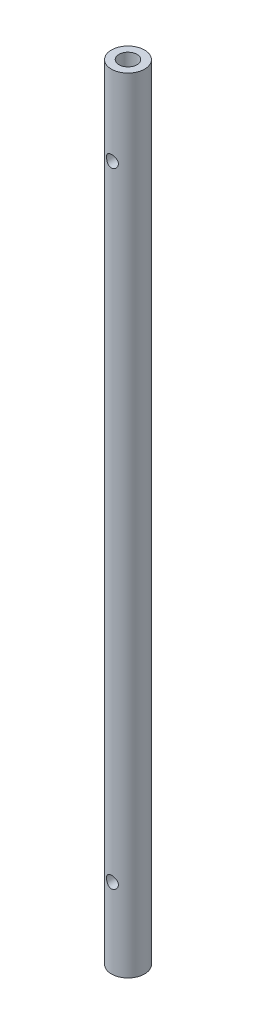
SolidWorks part; units mm, degrees
material "1060 Alloy"
ref_plane "Front Plane" through (0, 0, 0) normal (0, 0, 1) x (1, 0, 0)
ref_plane "Top Plane" through (0, 0, 0) normal (0, 1, 0) x (1, 0, 0)
ref_plane "Right Plane" through (0, 0, 0) normal (1, 0, 0) x (0, 0, -1)
sketch "Sketch1" plane through (0, 0, 0) normal (0, 1, 0) x (1, 0, 0)
  circle A0 centre (0, 0) radius 3.175
  dimension "D1" = 6.35
extrude "Boss-Extrude1" add sketch "Sketch1" along normal blind 149.86
hole_wizard "#8-32 Tapped Hole1" positions "Sketch3" profile "Sketch2" tap size "#8-32" standard "ANSI Inch"
sketch "Sketch3" plane through (0, 0, 0) normal (0, -1, 0) x (-1, 0, 0)
  point P0 (0, 0)
sketch "Sketch2" plane through (0, 0, 0) normal (1, 0, 0) x (0, 0, -1)
  line L0 (0, 0) -> (0, 13.7378)
  line L1 (0, 13.7378) -> (1.7272, 12.7)
  line L2 (1.7272, 12.7) -> (1.7272, 0)
  line L5 (1.7272, 0) -> (0, 0)
  line L10 (0, 13.7378) -> (-1.7272, 12.7) construction
  line L11 (0, -6.35) -> (0, 107.95) construction
  dimension "Tap Drill Dia." = 3.4544
  dimension "Tap Drill Depth" = 12.7
  dimension "Drill Angle" = 118
cosmetic thread "Hole Thread1" parameters "D1"=12.7, "D2"=4.1656
hole_wizard "#8-32 Tapped Hole2" positions "Sketch5" profile "Sketch4" tap size "#8-32" standard "ANSI Inch"
sketch "Sketch5" plane through (0, 149.86, 0) normal (0, 1, 0) x (1, 0, 0)
  point P0 (0, 0)
sketch "Sketch4" plane through (0, 149.86, 0) normal (1, 0, 0) x (0, 0, 1)
  line L0 (0, 0) -> (0, 16.1254)
  line L1 (0, 16.1254) -> (1.7272, 15.0876)
  line L2 (1.7272, 15.0876) -> (1.7272, 0)
  line L5 (1.7272, 0) -> (0, 0)
  line L10 (0, 16.1254) -> (-1.7272, 15.0876) construction
  line L11 (0, -6.35) -> (0, 107.95) construction
  dimension "Tap Drill Dia." = 3.4544
  dimension "Tap Drill Depth" = 15.0876
  dimension "Drill Angle" = 118
cosmetic thread "Hole Thread2" parameters "D1"=12.7, "D2"=4.1656
sketch "Sketch6" plane through (0, 0, 0) normal (0, 0, 1) x (1, 0, 0)
  line L0 (0, 149.86) -> (0, 134.62) construction
  line L1 (1.7272, 149.86) -> (-1.7272, 149.86) construction
  line L2 (0, 0) -> (0, 15.24) construction
  circle A0 centre (0, 134.62) radius 1.1303
  circle A1 centre (0, 15.24) radius 1.1303
  dimension "D3" = 2.2606
  dimension "D4" = 2.2606
  dimension "D1" = 15.24
  dimension "D2" = 15.24
extrude "Cut-Extrude1" cut sketch "Sketch6" against normal through all and the other way through all
